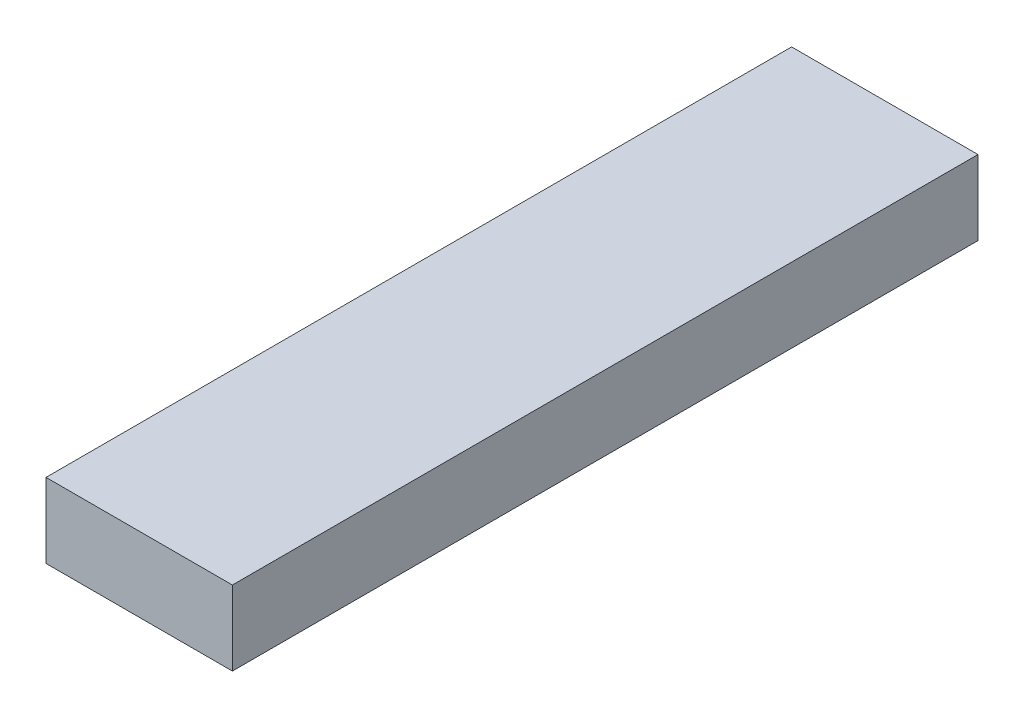
SolidWorks part; units mm, degrees
ref_plane "Alzado" through (0, 0, 0) normal (0, 0, 1) x (1, 0, 0)
ref_plane "Planta" through (0, 0, 0) normal (0, 1, 0) x (1, 0, 0)
ref_plane "Vista lateral" through (0, 0, 0) normal (1, 0, 0) x (0, 0, -1)
sketch "Croquis1" plane through (0, 0, 0) normal (0, 0, 1) x (1, 0, 0)
  line L1 (0, 0) -> (0.5, 0)
  line L2 (0, 0) -> (0, 0.2)
  line L3 (0, 0.2) -> (0.5, 0.2)
  line L4 (0.5, 0) -> (0.5, 0.2)
  dimension "D1" = 0.2
  dimension "D2" = 0.5
extrude "Saliente-Extruir1" add sketch "Croquis1" along normal blind 2
